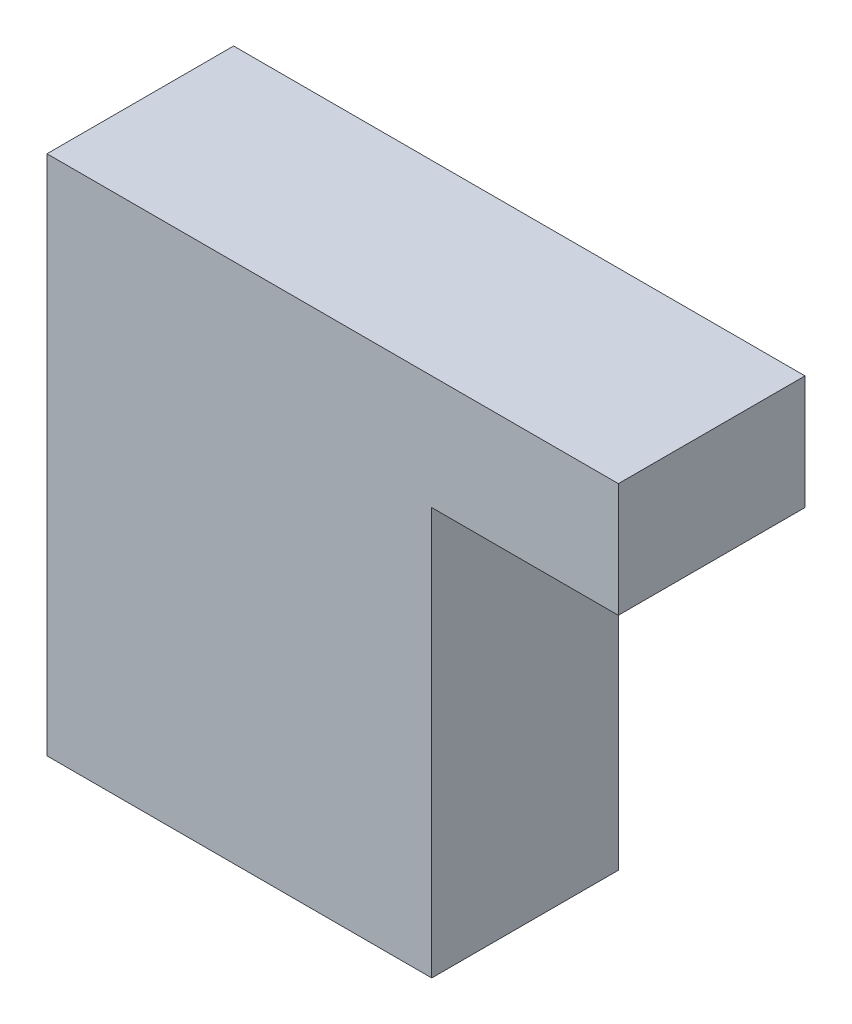
SolidWorks part; units mm, degrees
ref_plane "Ebene vorne" through (0, 0, 0) normal (0, 0, 1) x (1, 0, 0)
ref_plane "Ebene oben" through (0, 0, 0) normal (0, 1, 0) x (1, 0, 0)
ref_plane "Ebene rechts" through (0, 0, 0) normal (1, 0, 0) x (0, 0, -1)
sketch "Skizze1" plane through (0, 0, 0) normal (0, 0, 1) x (1, 0, 0)
  line L1 (0, 0) -> (20.6158, 0)
  line L2 (0, 0) -> (0, -27.9399)
  line L3 (0, -27.9399) -> (20.6158, -27.9399)
  line L4 (20.6158, 0) -> (20.6158, -27.9399)
extrude "Aufsatz-Linear austragen1" add sketch "Skizze1" along normal blind 10
sketch "Skizze2" plane through (0, 0, 10) normal (0, 0, 1) x (1, 0, 0)
  circle A0 centre (10.0314, -11.8384) radius 2.3913
sketch "Skizze3" plane through (20.6158, 0, 0) normal (1, 0, 0) x (0, 0, -1)
  line L0 (0, -27.9399) -> (0, 0) construction
  line L1 (-10, 0) -> (0, 0)
  line L2 (-10, 0) -> (-10, -6.1104)
  line L3 (-10, -6.1104) -> (0, -6.1104)
  line L4 (0, 0) -> (0, -6.1104)
extrude "Aufsatz-Linear austragen2" add sketch "Skizze3" along normal blind 10
